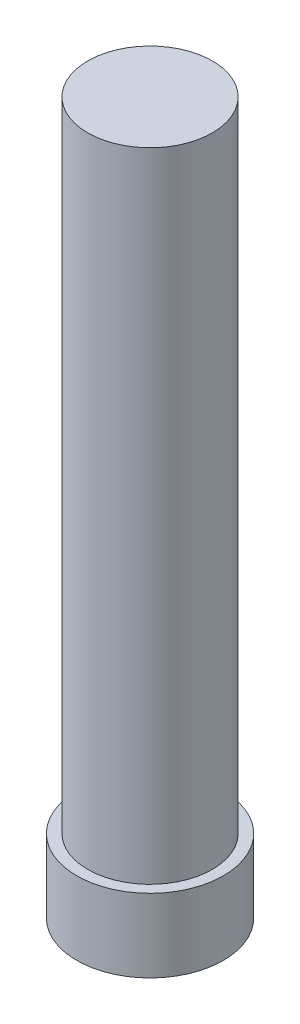
SolidWorks part; units mm, degrees
ref_plane "前视基准面" through (0, 0, 0) normal (0, 0, 1) x (1, 0, 0)
ref_plane "上视基准面" through (0, 0, 0) normal (0, 1, 0) x (1, 0, 0)
ref_plane "右视基准面" through (0, 0, 0) normal (1, 0, 0) x (0, 0, -1)
other "Configuration Table"
sketch "草图2" plane through (0, 0, 0) normal (0, 1, 0) x (1, 0, 0)
  circle A0 centre (0, 0) radius 0.85
  dimension "D1" = 1.7
extrude "凸台-拉伸1" add sketch "草图2" along normal blind 8.7
sketch "草图3" plane through (0, 0, 0) normal (0, -1, 0) x (1, 0, 0)
  circle A0 centre (0, 0) radius 1
  dimension "D1" = 2
extrude "凸台-拉伸2" add sketch "草图3" along normal blind 1
